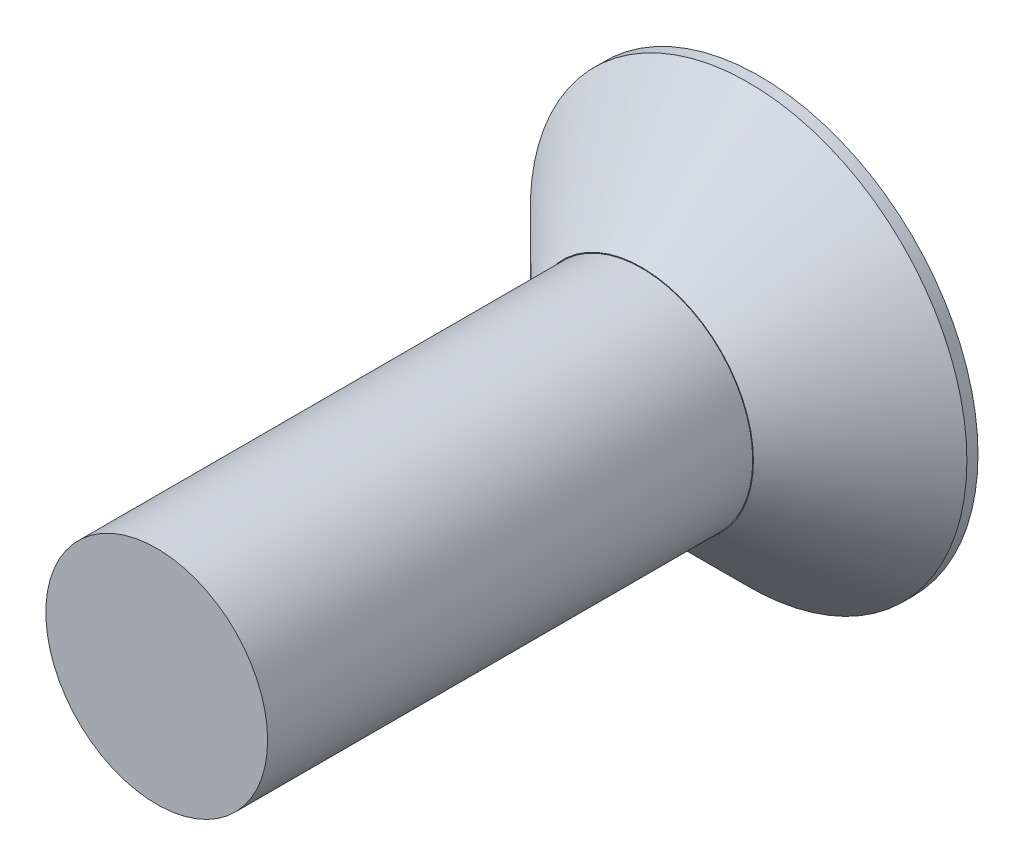
SolidWorks part; units mm, degrees
ref_plane "Front Plane" through (0, 0, 0) normal (0, 0, 1) x (1, 0, 0)
ref_plane "Top Plane" through (0, 0, 0) normal (0, 1, 0) x (1, 0, 0)
ref_plane "Right Plane" through (0, 0, 0) normal (1, 0, 0) x (0, 0, -1)
sketch "Sketch1" plane through (0, 0, 0) normal (0, 0, 1) x (1, 0, 0)
  circle A0 centre (0, 0) radius 4.0005
  dimension "D1" = 8.001
extrude "Extrude1" add sketch "Sketch1" along normal blind 2.159
sketch "Sketch2" plane through (0, 0, 2.159) normal (0, 0, 1) x (1, 0, 0)
  circle A0 centre (0, 0) radius 2.032
extrude "Extrude2" add sketch "Sketch2" along normal blind 8.89
sketch "Sketch3" plane through (0, 0, 0) normal (0, 0, -1) x (-1, 0, 0)
  line L1 (1.206, 0.66) -> (0.0314, 1.3745)
  line L2 (0.0314, 1.3745) -> (-1.1746, 0.7145)
  line L3 (-1.1746, 0.7145) -> (-1.206, -0.66)
  line L4 (-1.206, -0.66) -> (-0.0314, -1.3745)
  line L5 (-0.0314, -1.3745) -> (1.1746, -0.7145)
  line L6 (1.1746, -0.7145) -> (1.206, 0.66)
  circle A0 centre (0, 0) radius 1.1906 construction
  dimension "D1" = 2.3813
extrude "Extrude3" cut sketch "Sketch3" against normal blind 1.016
chamfer "Chamfer1" distance 1.9558 angle 45 1 edges at (4.0005, 0, 2.159)
